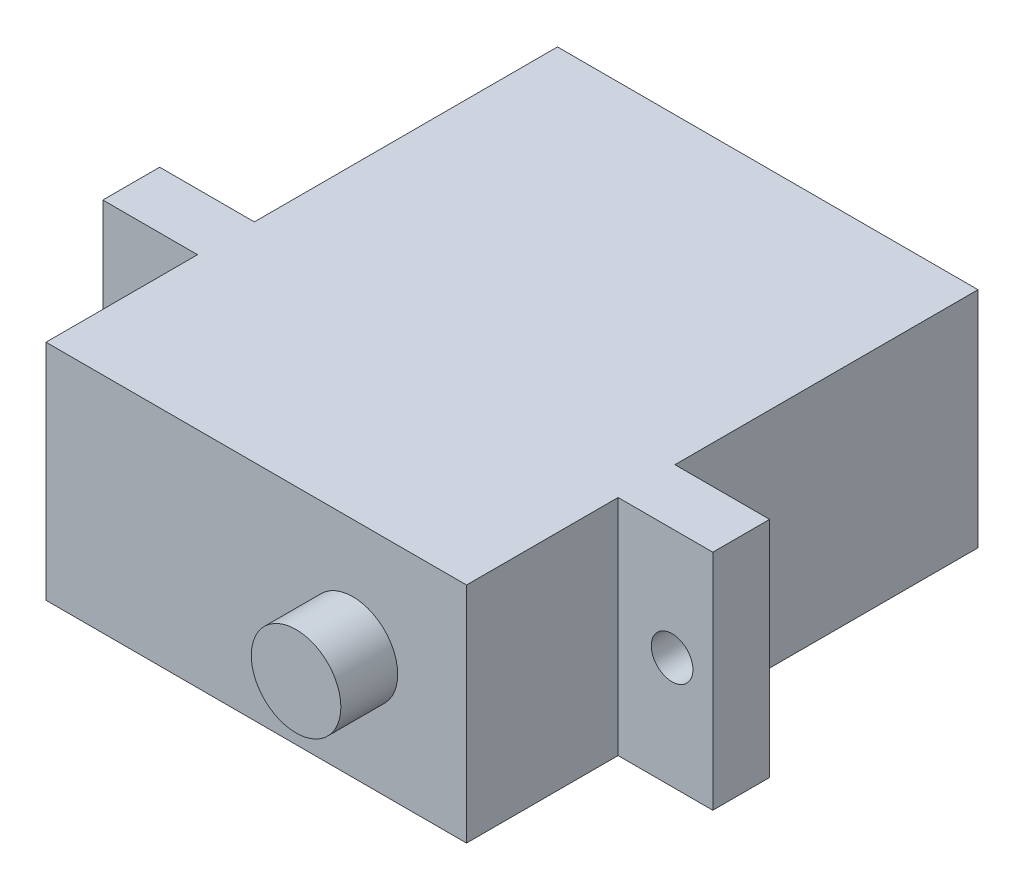
SolidWorks part; units mm, degrees
ref_plane "Front Plane" through (0, 0, 0) normal (0, 0, 1) x (1, 0, 0)
ref_plane "Top Plane" through (0, 0, 0) normal (0, 1, 0) x (1, 0, 0)
ref_plane "Right Plane" through (0, 0, 0) normal (1, 0, 0) x (0, 0, -1)
sketch "Sketch1" plane through (0, 0, 0) normal (0, 0, 1) x (1, 0, 0)
  line L0 (-16.1, 0) -> (16.1, 0)
  line L1 (16.1, 0) -> (16.1, 11.8)
  line L2 (16.1, 11.8) -> (-16.1, 11.8)
  line L3 (-16.1, 11.8) -> (-16.1, 0)
  point P4 (0, 0)
  dimension "D1" = 32.2
  dimension "D2" = 11.8
extrude "Boss-Extrude1" add sketch "Sketch1" against normal blind 27
sketch "Sketch2" plane through (0, 0, 0) normal (0, 0, 1) x (1, 0, 0)
  line L0 (16.1, 5.9) -> (5.1, 5.9) construction
  line L1 (16.1, 0) -> (16.1, 11.8) construction
  circle A0 centre (5.1, 5.9) radius 2.365
  dimension "D2" = 4.73
  dimension "D1" = 11
extrude "Boss-Extrude2" add sketch "Sketch2" along normal blind 3
sketch "Sketch4" plane through (16.1, 0, 0) normal (1, 0, 0) x (0, 0, -1)
  line L0 (27, 11.8) -> (0, 11.8) construction
  line L1 (27, 11.8) -> (11, 11.8)
  line L2 (27, 11.8) -> (27, 0)
  line L3 (27, 0) -> (11, 0)
  line L4 (11, 11.8) -> (11, 0)
  line L5 (27, 0) -> (27, 11.8) construction
  line L6 (27, 0) -> (0, 0) construction
  dimension "D1" = 16
extrude "Cut-Extrude1" cut sketch "Sketch4" against normal blind 5
sketch "Sketch5" plane through (-16.1, 0, 0) normal (-1, 0, 0) x (0, 0, 1)
  line L0 (-27, 0) -> (0, 0) construction
  line L1 (-27, 11.8) -> (-11, 11.8)
  line L2 (-27, 11.8) -> (-27, 0)
  line L3 (-27, 0) -> (-11, 0)
  line L4 (-11, 11.8) -> (-11, 0)
  dimension "D1" = 16
extrude "Cut-Extrude2" cut sketch "Sketch5" against normal blind 5
sketch "Sketch6" plane through (-16.1, 0, 0) normal (-1, 0, 0) x (0, 0, 1)
  line L0 (-11, 0) -> (0, 0) construction
  line L1 (0, 11.8) -> (-8, 11.8)
  line L2 (0, 11.8) -> (0, 0)
  line L3 (0, 0) -> (-8, 0)
  line L4 (-8, 11.8) -> (-8, 0)
  line L5 (-11, 0) -> (-11, 11.8) construction
  dimension "D1" = 3
extrude "Cut-Extrude3" cut sketch "Sketch6" against normal blind 5
sketch "Sketch7" plane through (16.1, 0, 0) normal (1, 0, 0) x (0, 0, -1)
  line L0 (11, 0) -> (0, 0) construction
  line L1 (0, 11.8) -> (8, 11.8)
  line L2 (0, 11.8) -> (0, 0)
  line L3 (0, 0) -> (8, 0)
  line L4 (8, 11.8) -> (8, 0)
  line L5 (11, 11.8) -> (11, 0) construction
  dimension "D1" = 3
extrude "Cut-Extrude4" cut sketch "Sketch7" against normal blind 5
sketch "Sketch8" plane through (0, 0, -8) normal (0, 0, 1) x (1, 0, 0)
  line L0 (16.1, 0) -> (16.1, 11.8) construction
  line L4 (16.1, 11.8) -> (16.1, 0) construction
  line L5 (0, 0) -> (0, 11.8) construction
  line L6 (11.1, 11.8) -> (-11.1, 11.8) construction
  circle A0 centre (13.95, 5.9) radius 1.1
  circle A1 centre (-13.95, 5.9) radius 1.1
  point P8 (16.1, 5.9)
  dimension "D1" = 2.2
  dimension "D2" = 2.15
extrude "Cut-Extrude5" cut sketch "Sketch8" against normal up to next
sketch "Sketch9" [suppressed] plane through (0, 0, -8) normal (0, 0, 1) x (1, 0, 0)
  line L0 (-13.95, 5.9) -> (-13.95, 11.8) construction
  line L1 (-11.1, 11.8) -> (-16.1, 11.8) construction
